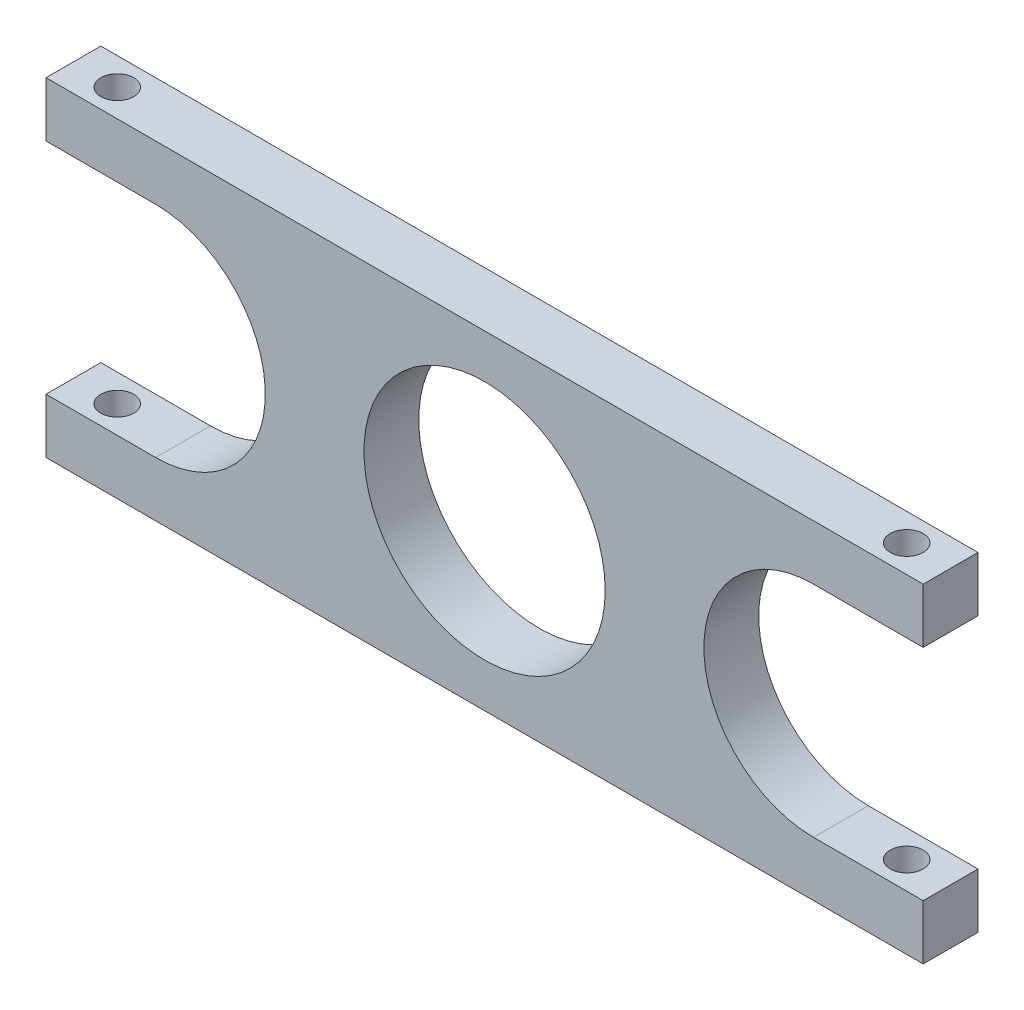
SolidWorks part; units mm, degrees
material "ABS"
ref_plane "Plan de face" through (0, 0, 0) normal (0, 0, 1) x (1, 0, 0)
ref_plane "Plan de dessus" through (0, 0, 0) normal (0, 1, 0) x (1, 0, 0)
ref_plane "Plan de droite" through (0, 0, 0) normal (1, 0, 0) x (0, 0, -1)
sketch "Esquisse1" plane through (0, 0, 0) normal (0, 0, 1) x (1, 0, 0)
  line L0 (0, 0) -> (80, 0)
  line L1 (80, 0) -> (80, 5)
  line L2 (80, 5) -> (70, 5)
  line L4 (70, 25) -> (80, 25)
  line L5 (80, 25) -> (80, 30)
  line L6 (80, 30) -> (0, 30)
  line L7 (0, 30) -> (0, 25)
  line L8 (0, 25) -> (10, 25)
  line L10 (10, 5) -> (0, 5)
  line L11 (0, 5) -> (0, 0)
  arc A0 (10, 25) -> (10, 5) centre (10, 15) cw
  arc A1 (70, 25) -> (70, 5) centre (70, 15) ccw
  circle A2 centre (40, 15) radius 11
  dimension "D10" = 22
  dimension "D1" = 80
  dimension "D2" = 80
  dimension "D3" = 10
  dimension "D4" = 10
  dimension "D5" = 30
  dimension "D6" = 5
  dimension "D7" = 5
  dimension "D8" = 5
  dimension "D9" = 5
  dimension "D11" = 15
  dimension "D12" = 40
extrude "Boss.-Extru.1" add sketch "Esquisse1" along normal blind 5
hole_wizard "Dégagement M31" positions "Esquisse2" profile "Esquisse3" hole size "M3" standard "ISO" end condition through all
sketch "Esquisse2" plane through (0, 30, 0) normal (0, 1, 0) x (1, 0, 0)
  line L0 (80, 0) -> (0, 0) construction
  line L1 (0, -5) -> (0, 0) construction
  line L2 (80, -5) -> (0, -5) construction
  line L3 (80, -5) -> (80, 0) construction
  point P0 (4, -2.5)
  point P2 (76, -2.5)
  dimension "D1" = 2.5
  dimension "D2" = 4
  dimension "D3" = 2.5
  dimension "D4" = 4
sketch "Esquisse3" plane through (4, 30, 2.5) normal (1, 0, 0) x (0, 0, 1)
  line L0 (0, 0) -> (0, 30)
  line L1 (0, 30) -> (1.5, 30)
  line L2 (1.5, 30) -> (1.5, 0)
  line L5 (1.5, 0) -> (0, 0)
  line L11 (0, -6.35) -> (0, 107.95) construction
  dimension "Diamètre du perçage jusqu'au prochain" = 3
  dimension "Profondeur du perçage jusqu'au prochain" = 30
